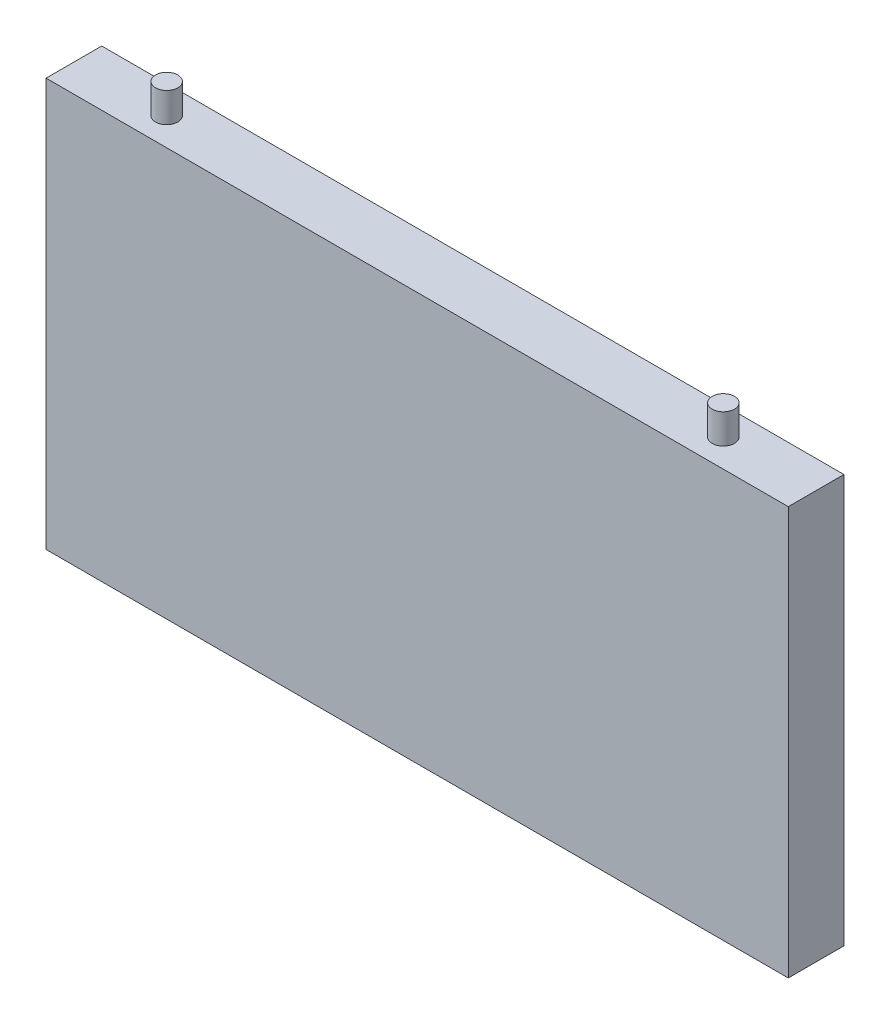
SolidWorks part; units mm, degrees
ref_plane "Plano frontal" through (0, 0, 0) normal (0, 0, 1) x (1, 0, 0)
ref_plane "Plano superior" through (0, 0, 0) normal (0, 1, 0) x (1, 0, 0)
ref_plane "Plano direito" through (0, 0, 0) normal (1, 0, 0) x (0, 0, -1)
sketch "Esboço1" plane through (0, 0, 0) normal (0, 0, 1) x (1, 0, 0)
  line L1 (0, 0) -> (200, 0)
  line L2 (0, 0) -> (0, 110)
  line L3 (0, 110) -> (200, 110)
  line L4 (200, 0) -> (200, 110)
extrude "Ressalto-extrusão1" add sketch "Esboço1" along normal blind 15
sketch "Esboço2" plane through (0, 110, 0) normal (0, 1, 0) x (1, 0, 0)
  line L0 (0, -7.5) -> (25, -7.5)
  line L1 (0, -15) -> (0, 0) construction
  point P5 (25, -7.5)
sketch "Esboço7" plane through (0, 110, 0) normal (0, 1, 0) x (1, 0, 0)
  line L0 (200, -7.5) -> (175, -7.5)
  line L1 (200, -15) -> (200, 0) construction
  line L2 (0, -7.5) -> (25, -7.5)
  line L3 (0, -15) -> (0, 0) construction
  circle A0 centre (175, -7.5) radius 3
  circle A1 centre (25, -7.5) radius 3
extrude "Ressalto-extrusão2" add sketch "Esboço7" along normal blind 8
